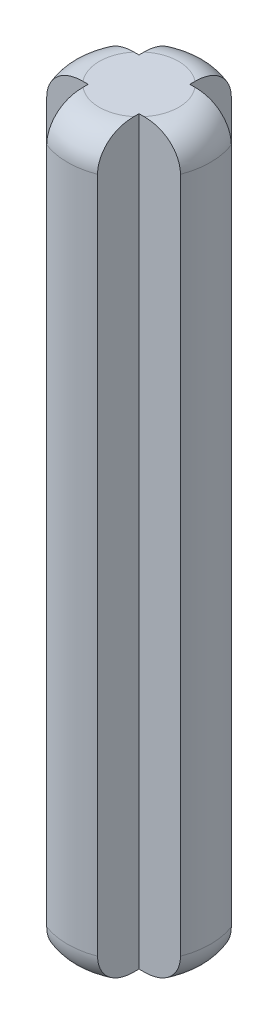
SolidWorks part; units mm, degrees
ref_plane "Front Plane" through (0, 0, 0) normal (0, 0, 1) x (1, 0, 0)
ref_plane "Top Plane" through (0, 0, 0) normal (0, 1, 0) x (1, 0, 0)
ref_plane "Right Plane" through (0, 0, 0) normal (1, 0, 0) x (0, 0, -1)
sketch "Sketch1" plane through (0, 0, 0) normal (0, 1, 0) x (1, 0, 0)
  line L0 (-0.8, -0.8) -> (-0.8, -2.103)
  line L1 (-0.8, 0.8) -> (-2.103, 0.8)
  line L2 (2.103, 0.8) -> (0.8, 0.8)
  line L3 (2.103, -0.8) -> (0.8, -0.8)
  line L4 (0.8, -0.8) -> (0.8, -2.103)
  line L5 (-0.8, -0.8) -> (-2.103, -0.8)
  line L6 (-7.75, 0) -> (-7.75, 0)
  line L7 (-7.75, 0) -> (-7.75, 0)
  line L8 (-0.8, 2.103) -> (-0.8, 0.8)
  line L9 (0.8, 2.103) -> (0.8, 0.8)
  line L10 (-7.75, 0) -> (-7.75, 0)
  line L11 (7.75, 0) -> (7.75, 0)
  line L12 (7.75, 0) -> (7.75, 0)
  line L13 (7.75, 0) -> (7.75, 0)
  line L14 (7.75, 0) -> (7.75, 0)
  line L15 (-7.75, 0) -> (-7.75, 0)
  line L16 (-8.6621, 8.6621) -> (-8.6621, 8.6621)
  line L17 (-8.6621, -8.6621) -> (-8.6621, -8.6621)
  line L18 (-8.6621, -8.6621) -> (-8.6621, -8.6621)
  line L19 (8.6621, -8.6621) -> (8.6621, -8.6621)
  line L20 (8.6621, -8.6621) -> (8.6621, -8.6621)
  line L21 (8.6621, 8.6621) -> (8.6621, 8.6621)
  line L22 (8.6621, 8.6621) -> (8.6621, 8.6621)
  line L23 (-8.6621, 8.6621) -> (-8.6621, 8.6621)
  arc A0 (-2.103, 0.8) -> (-2.103, -0.8) centre (0, 0) ccw
  arc A1 (0.8, 2.103) -> (-0.8, 2.103) centre (0, 0) ccw
  arc A2 (2.103, -0.8) -> (2.103, 0.8) centre (0, 0) ccw
  arc A3 (-0.8, -2.103) -> (0.8, -2.103) centre (0, 0) ccw
  arc A4 (-7.75, 0) -> (-7.75, 0) centre (-7.75, 0) ccw
  arc A5 (-7.75, 0) -> (7.75, 0) centre (0, 0) ccw
  arc A6 (7.75, 0) -> (7.75, 0) centre (7.75, 0) ccw
  arc A7 (7.75, 0) -> (-7.75, 0) centre (0, 0) ccw
  arc A8 (-8.6621, 8.6621) -> (-8.6621, -8.6621) centre (0, 0) ccw
  arc A9 (-8.6621, -8.6621) -> (8.6621, -8.6621) centre (0, 0) ccw
  arc A10 (8.6621, -8.6621) -> (8.6621, 8.6621) centre (0, 0) ccw
  arc A11 (8.6621, 8.6621) -> (-8.6621, 8.6621) centre (0, 0) ccw
  point P26 (0.8, 0)
  dimension "D1" = 4.5
  dimension "D2" = 10
  dimension "D3" = 10
extrude "Boss-Extrude1" add sketch "Sketch1" along normal offset from surface (23.3 mm away) 23.3 contours L0 A3 L4 L3 A2 L2 L9 A1 L8 L1 A0 L5 up to plane "Top Plane"
fillet "Fillet1" radius 1 1 edges at (-2.25, 0, 0)
fillet "Fillet2" radius 1 1 edges at (0, 0, 2.25)
fillet "Fillet3" radius 1 1 edges at (2.25, 0, 0)
fillet "Fillet4" radius 1 1 edges at (0, 0, -2.25)
fillet "Fillet20" radius 1 1 edges at (2.25, 23.3, 0)
fillet "Fillet21" radius 1 1 edges at (0, 23.3, 2.25)
fillet "Fillet22" radius 1 1 edges at (-2.25, 23.3, 0)
fillet "Fillet23" radius 1 1 edges at (0, 23.3, -2.25)
